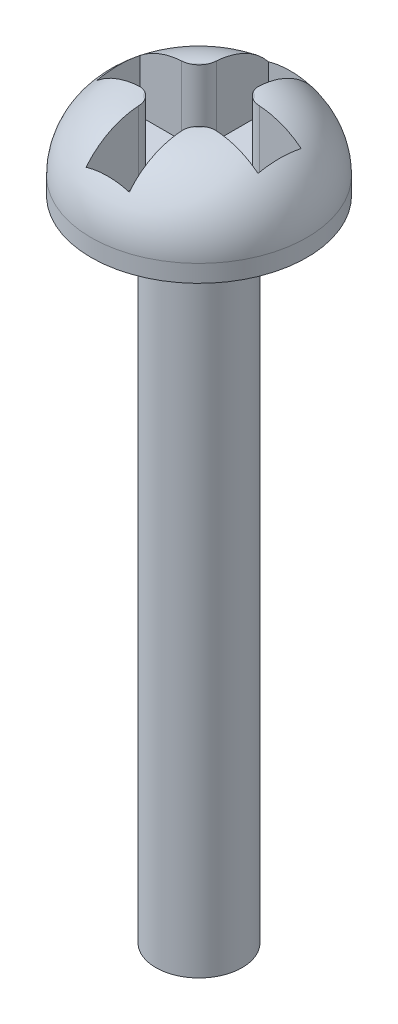
SolidWorks part; units mm, degrees
ref_plane "Front Plane" through (0, 0, 0) normal (0, 0, 1) x (1, 0, 0)
ref_plane "Top Plane" through (0, 0, 0) normal (0, 1, 0) x (1, 0, 0)
ref_plane "Right Plane" through (0, 0, 0) normal (1, 0, 0) x (0, 0, -1)
sketch "Sketch1" plane through (0, 0, 0) normal (0, 1, 0) x (1, 0, 0)
  circle A0 centre (0, 0) radius 1.27
  dimension "D1" = 2.54
extrude "Boss-Extrude1" add sketch "Sketch1" along normal mid plane 19.05
sketch "Sketch2" plane through (0, 9.525, 0) normal (0, 1, 0) x (1, 0, 0)
  circle A0 centre (0, 0) radius 3.175
  dimension "D1" = 6.35
extrude "Boss-Extrude2" add sketch "Sketch2" along normal blind 2.54
fillet "Fillet1" radius 2.032 1 edges at (0, 12.065, 3.175)
sketch "Sketch3" plane through (0, 12.065, 0) normal (0, 1, 0) x (1, 0, 0)
  line L0 (-0.635, 1.143) -> (-0.635, 2.6854)
  line L1 (-2.3713, 0.635) -> (-1.143, 0.635)
  line L2 (-2.3713, 0.635) -> (-2.3713, -0.635)
  line L3 (-2.3713, -0.635) -> (-1.143, -0.635)
  line L4 (2.3713, 0.635) -> (2.3713, -0.635)
  line L5 (-2.3713, 0.635) -> (2.3713, -0.635) construction
  line L6 (-2.3713, -0.635) -> (2.3713, 0.635) construction
  line L7 (-0.635, -2.6854) -> (0.635, -2.6854)
  line L8 (-0.635, -2.6854) -> (-0.635, -1.143)
  line L9 (-0.635, 2.6854) -> (0.635, 2.6854)
  line L10 (0.635, -2.6854) -> (0.635, -1.143)
  line L11 (-0.635, -2.6854) -> (0.635, 2.6854) construction
  line L12 (-0.635, 2.6854) -> (0.635, -2.6854) construction
  line L13 (1.143, 0.635) -> (2.3713, 0.635)
  line L14 (0.635, 1.143) -> (0.635, 2.6854)
  line L15 (1.143, -0.635) -> (2.3713, -0.635)
  circle A0 centre (0, 0) radius 3.175 construction
  arc A1 (-0.635, 1.143) -> (-1.143, 0.635) centre (-1.143, 1.143) cw
  arc A2 (-1.143, -0.635) -> (-0.635, -1.143) centre (-1.143, -1.143) cw
  arc A3 (0.635, -1.143) -> (1.143, -0.635) centre (1.143, -1.143) cw
  arc A4 (1.143, 0.635) -> (0.635, 1.143) centre (1.143, 1.143) cw
  point P0 (0, 0)
  point P6 (0, 0)
  point P23 (0.635, -0.635)
  point P26 (0.635, 0.635)
  dimension "D3" = 0.508
  dimension "D4" = 0.508
  dimension "D5" = 0.508
  dimension "D6" = 0.508
  dimension "D1" = 2.3713
  dimension "D2" = 1.27
extrude "Cut-Extrude1" cut sketch "Sketch3" against normal blind 2.032
